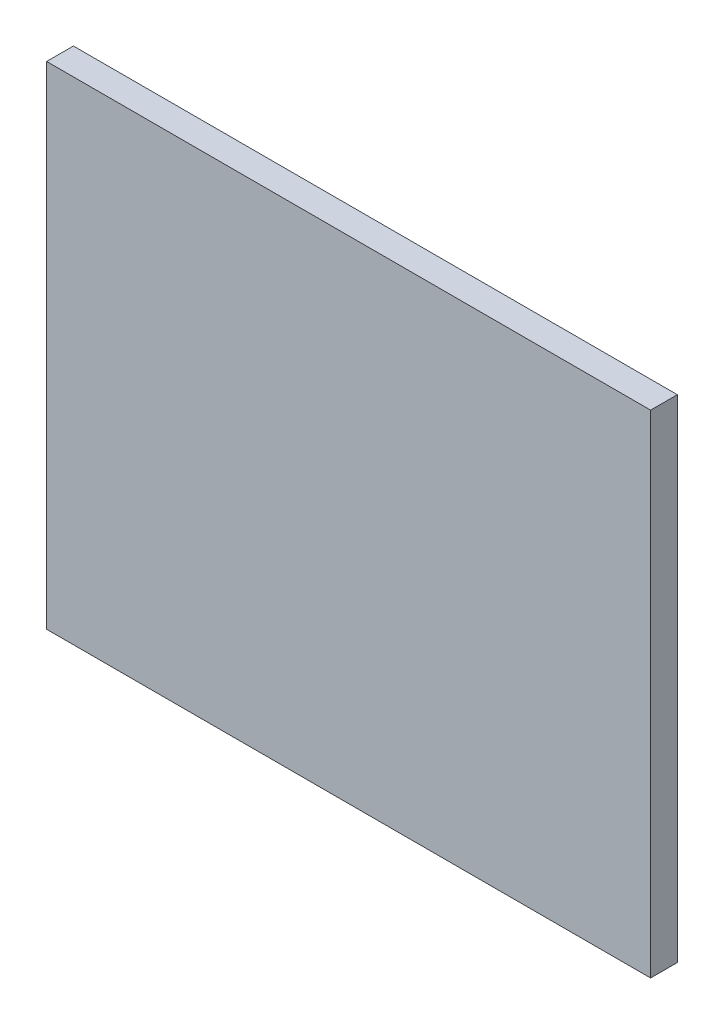
SolidWorks part; units mm, degrees
ref_plane "Front Plane" through (0, 0, 0) normal (0, 0, 1) x (1, 0, 0)
ref_plane "Top Plane" through (0, 0, 0) normal (0, 1, 0) x (1, 0, 0)
ref_plane "Right Plane" through (0, 0, 0) normal (1, 0, 0) x (0, 0, -1)
sketch "Sketch1" plane through (0, 0, 0) normal (0, 0, 1) x (1, 0, 0)
  line L1 (-105, -85.5) -> (105, -85.5)
  line L2 (-105, -85.5) -> (-105, 85.5)
  line L3 (-105, 85.5) -> (105, 85.5)
  line L4 (105, -85.5) -> (105, 85.5)
  line L5 (-105, -85.5) -> (105, 85.5) construction
  line L6 (-105, 85.5) -> (105, -85.5) construction
  point P0 (0, 0)
  dimension "D1" = 171
  dimension "D2" = 210
extrude "Boss-Extrude1" add sketch "Sketch1" along normal blind 9.3
sketch "Sketch2" plane through (0, -85.5, 0) normal (0, -1, 0) x (1, 0, 0)
  line L0 (0, 49.8671) -> (0, -71.6466) construction
ref_plane "Plane1" through (0, -15.5, 0) normal (0, -1, 0) x (-1, 0, 0)
sketch "Sketch3" plane through (0, -15.5, 0) normal (0, -1, 0) x (-1, 0, 0)
  line L0 (0, 106.8827) -> (0, -87.21) construction
sketch "Sketch4" plane through (0, 85.5, 0) normal (0, 1, 0) x (1, 0, 0)
  line L0 (-124.3036, -4.65) -> (125.0937, -4.65) construction
sketch "Sketch5" plane through (0, -85.5, 0) normal (0, -1, 0) x (1, 0, 0)
  line L0 (-124.3036, 4.65) -> (125.0937, 4.65) construction
